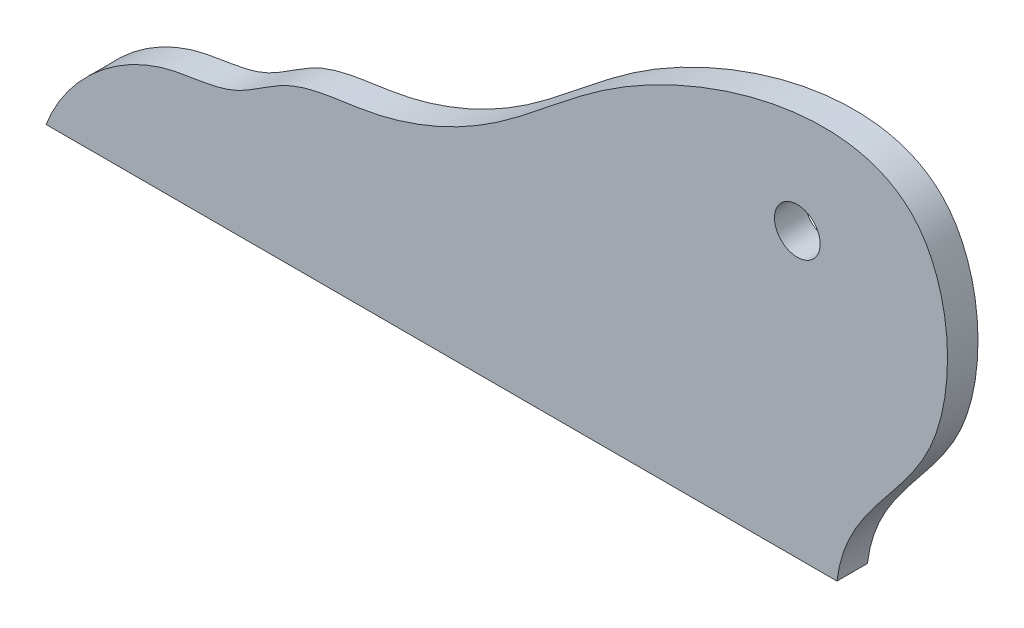
SolidWorks part; units mm, degrees
ref_plane "Front Plane" through (0, 0, 0) normal (0, 0, 1) x (1, 0, 0)
ref_plane "Top Plane" through (0, 0, 0) normal (0, 1, 0) x (1, 0, 0)
ref_plane "Right Plane" through (0, 0, 0) normal (1, 0, 0) x (0, 0, -1)
sketch "Sketch1" plane through (0, 0, 0) normal (0, 0, 1) x (1, 0, 0)
  line L0 (302.5, 350) -> (1512.5, 350) construction
  line L1 (320.5291, 17.0632) -> (402.9532, 17.0632)
  circle A0 centre (398.8216, 46.6036) radius 2.3813
  spline S0 degree 3 poles (320.5291, 17.0632) (322.6027, 22.4221) (329.5694, 28.8033) (340.1819, 29.1027) (346.0343, 34.2898) (356.0872, 34.6666) (368.371, 40.2422) (381.8655, 53.8621) (414.2774, 63.7017) (415.9888, 31.2996) (403.8234, 24.4244) (402.9532, 17.0632) knots 0 0 0 0 0.12404 0.172266 0.219744 0.281543 0.380522 0.496241 0.71866 0.860485 1 1 1 1
  dimension "D24" = 4.7625
  dimension "D1" = 320.5291
  dimension "D2" = 321.9752
  dimension "D3" = 333.3369
  dimension "D4" = 339.9473
  dimension "D5" = 345.7315
  dimension "D6" = 354.2011
  dimension "D7" = 367.0088
  dimension "D8" = 380.0232
  dimension "D9" = 402.9532
  dimension "D10" = 407.7044
  dimension "D11" = 411.0096
  dimension "D12" = 412.6622
  dimension "D13" = 17.0632
  dimension "D14" = 19.9553
  dimension "D15" = 26.7723
  dimension "D16" = 28.4249
  dimension "D17" = 29.8709
  dimension "D18" = 33.1762
  dimension "D19" = 34.0025
  dimension "D20" = 35.0353
  dimension "D21" = 40.4063
  dimension "D22" = 50.1154
  dimension "D23" = 53.8338
extrude "Boss-Extrude1" add sketch "Sketch1" along normal blind 3.175
